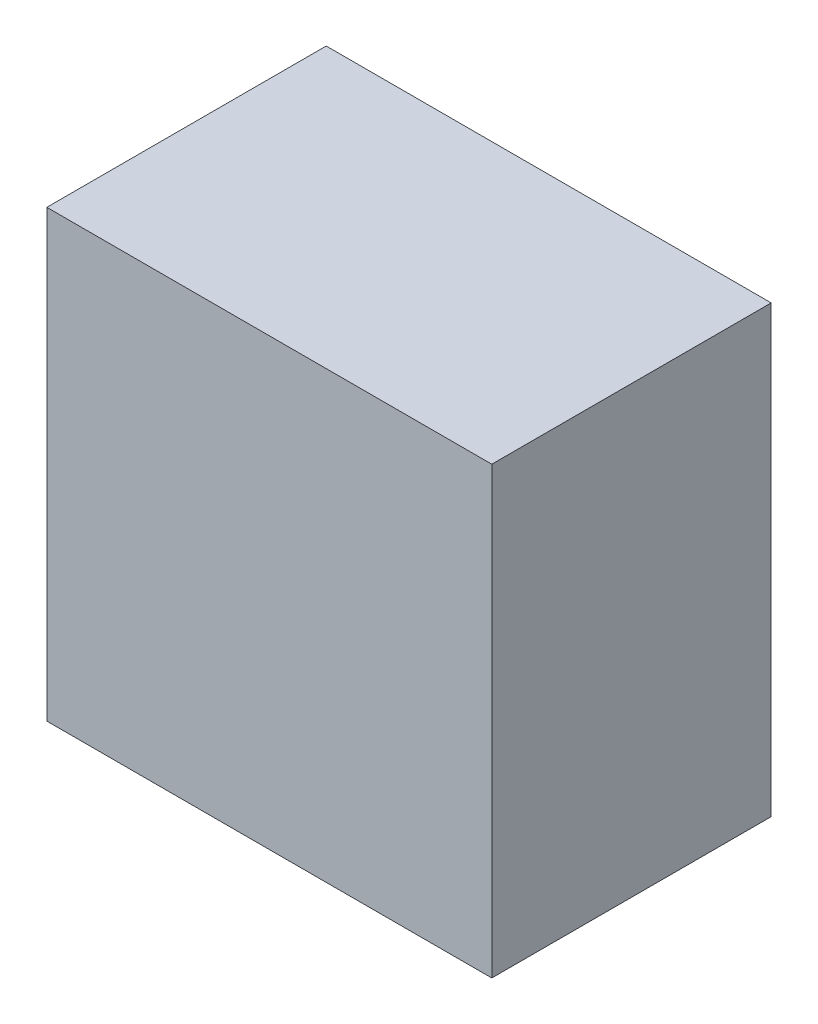
SolidWorks part; units mm, degrees
ref_plane "Front Plane" through (0, 0, 0) normal (0, 0, 1) x (1, 0, 0)
ref_plane "Top Plane" through (0, 0, 0) normal (0, 1, 0) x (1, 0, 0)
ref_plane "Right Plane" through (0, 0, 0) normal (1, 0, 0) x (0, 0, -1)
sketch "Sketch1" plane through (0, 0, 0) normal (0, 0, 1) x (1, 0, 0)
  line L1 (-21.5, -21.5) -> (21.5, -21.5)
  line L2 (-21.5, -21.5) -> (-21.5, 21.5)
  line L3 (-21.5, 21.5) -> (21.5, 21.5)
  line L4 (21.5, -21.5) -> (21.5, 21.5)
  line L5 (-21.5, -21.5) -> (21.5, 21.5) construction
  line L6 (-21.5, 21.5) -> (21.5, -21.5) construction
  point P0 (0, 0)
  dimension "D1" = 43
  dimension "D2" = 43
extrude "Boss-Extrude1" add sketch "Sketch1" along normal blind 27
